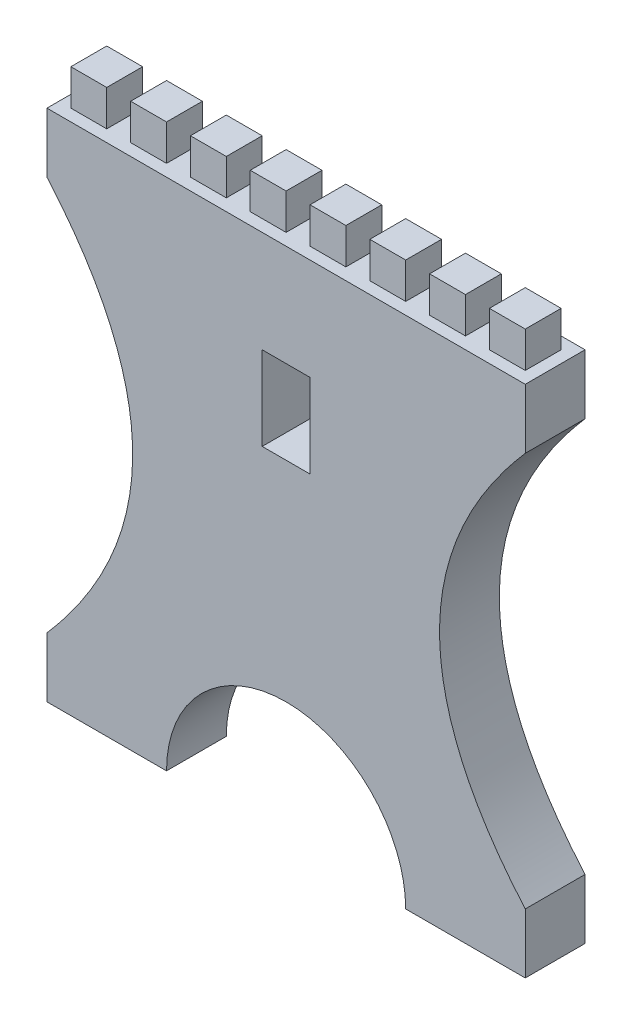
SolidWorks part; units mm, degrees
material "Дуб"
ref_plane "Спереди" through (0, 0, 0) normal (0, 0, 1) x (1, 0, 0)
ref_plane "Сверху" through (0, 0, 0) normal (0, 1, 0) x (1, 0, 0)
ref_plane "Справа" through (0, 0, 0) normal (1, 0, 0) x (0, 0, -1)
sketch "Эскиз1" plane through (0, 0, 0) normal (0, 0, 1) x (1, 0, 0)
  line L0 (0, 262.3394) -> (0, -266.7981) construction
  line L1 (-206.4251, 0) -> (195.8089, 0) construction
  line L2 (-100, -215) -> (-200, -215)
  line L3 (200, -215) -> (100, -215)
  line L4 (-200, -215) -> (-200, -165)
  line L5 (-200, 215) -> (0, 215)
  line L6 (-200, 215) -> (-200, 165)
  line L7 (200, -215) -> (-200, 215) construction
  line L8 (200, 215) -> (-200, -215) construction
  line L9 (0, 215) -> (200, 215)
  line L10 (-20, 130) -> (20, 130)
  line L11 (-20, 130) -> (-20, 60)
  line L12 (-20, 60) -> (20, 60)
  line L13 (20, 130) -> (20, 60)
  line L14 (-20, 130) -> (20, 60) construction
  line L15 (-20, 60) -> (20, 130) construction
  line L27 (200, 165) -> (200, 215)
  line L30 (200, -215) -> (200, -165)
  arc A0 (100, -215) -> (-100, -215) centre (0, -215) ccw
  spline S0 degree 2 poles (200, 165) (56.658, 0) (200, -165) knots 0 0 0 1 1 1
  spline S1 degree 2 poles (-200, 165) (-56.658, 0) (-200, -165) knots 0 0 0 1 1 1
  point P5 (0, 0)
  point P19 (0, 95)
  dimension "D3" = 100
  dimension "D5" = 215
  dimension "D1" = 430
  dimension "D2" = 400
  dimension "D4" = 50
  dimension "D6" = 40
  dimension "D7" = 70
  dimension "D8" = 60
  dimension "D13" = 50
  dimension "D14" = 100
extrude "Бобышка-Вытянуть3" add sketch "Эскиз1" along normal blind 50
sketch "Эскиз6" plane through (0, 215, 0) normal (0, 1, 0) x (1, 0, 0)
  line L0 (-200, -50) -> (-200, 0) construction
  line L1 (-190, -10) -> (-160, -10)
  line L2 (-190, -10) -> (-190, -40)
  line L3 (-190, -40) -> (-160, -40)
  line L4 (-160, -10) -> (-160, -40)
  line L5 (-190, -10) -> (-160, -40) construction
  line L6 (-190, -40) -> (-160, -10) construction
  line L7 (200, 0) -> (-200, 0) construction
  line L8 (200, -50) -> (200, 0) construction
  line L9 (-140, -10) -> (-110, -10)
  line L10 (-140, -10) -> (-140, -40)
  line L11 (-140, -40) -> (-110, -40)
  line L12 (-110, -10) -> (-110, -40)
  line L13 (-140, -10) -> (-110, -40) construction
  line L14 (-140, -40) -> (-110, -10) construction
  line L16 (-90, -10) -> (-60, -10)
  line L17 (-90, -10) -> (-90, -40)
  line L18 (-90, -40) -> (-60, -40)
  line L19 (-60, -10) -> (-60, -40)
  line L20 (-90, -10) -> (-60, -40) construction
  line L21 (-40, -10) -> (-10, -10)
  line L22 (-40, -10) -> (-40, -40)
  line L23 (-40, -40) -> (-10, -40)
  line L24 (-10, -10) -> (-10, -40)
  line L25 (-40, -10) -> (-10, -40) construction
  line L26 (-40, -40) -> (-10, -10) construction
  line L27 (10, -10) -> (40, -10)
  line L28 (10, -10) -> (10, -40)
  line L29 (10, -40) -> (40, -40)
  line L30 (40, -10) -> (40, -40)
  line L31 (10, -10) -> (40, -40) construction
  line L32 (10, -40) -> (40, -10) construction
  line L33 (60, -10) -> (90, -10)
  line L34 (60, -10) -> (60, -40)
  line L35 (60, -40) -> (90, -40)
  line L36 (90, -10) -> (90, -40)
  line L37 (60, -10) -> (90, -40) construction
  line L38 (60, -40) -> (90, -10) construction
  line L39 (110, -10) -> (140, -10)
  line L40 (110, -10) -> (110, -40)
  line L41 (110, -40) -> (140, -40)
  line L42 (140, -10) -> (140, -40)
  line L43 (110, -10) -> (140, -40) construction
  line L44 (110, -40) -> (140, -10) construction
  line L45 (160, -10) -> (190, -10)
  line L46 (160, -10) -> (160, -40)
  line L47 (160, -40) -> (190, -40)
  line L48 (190, -10) -> (190, -40)
  line L49 (160, -10) -> (190, -40) construction
  line L50 (160, -40) -> (190, -10) construction
  line L51 (200, -50) -> (-200, -50) construction
  line L52 (-90, -40) -> (-60, -10) construction
  point P0 (-175, -25)
  point P5 (-200, -25)
  point P10 (-125, -25)
  point P15 (-80.2103, -19.7897)
  point P16 (-75, -25)
  point P20 (-25, -25)
  point P25 (25, -25)
  point P30 (75, -25)
  point P35 (125, -25)
  point P40 (175, -25)
  dimension "D1" = 30
  dimension "D2" = 30
  dimension "D3" = 10
  dimension "D4" = 10
  dimension "D5" = 30
  dimension "D6" = 30
  dimension "D7" = 20
  dimension "D8" = 30
  dimension "D9" = 10
  dimension "D10" = 30
  dimension "D11" = 30
  dimension "D12" = 10
  dimension "D13" = 20
  dimension "D14" = 10
  dimension "D15" = 10
  dimension "D16" = 20
  dimension "D17" = 30
  dimension "D18" = 10
  dimension "D19" = 10
  dimension "D20" = 20
  dimension "D21" = 30
  dimension "D22" = 10
  dimension "D23" = 10
  dimension "D24" = 20
  dimension "D25" = 30
  dimension "D26" = 10
  dimension "D27" = 10
  dimension "D28" = 30
  dimension "D29" = 10
  dimension "D30" = 20
extrude "Бобышка-Вытянуть6" add sketch "Эскиз6" along normal blind 30 contours L10 L11 L12 L9 | L2 L3 L4 L1 | L28 L29 L30 L27 | L22 L23 L24 L21 | L17 L18 L19 L16 | L46 L47 L48 L45 | L40 L41 L42 L39 | L34 L35 L36 L33
